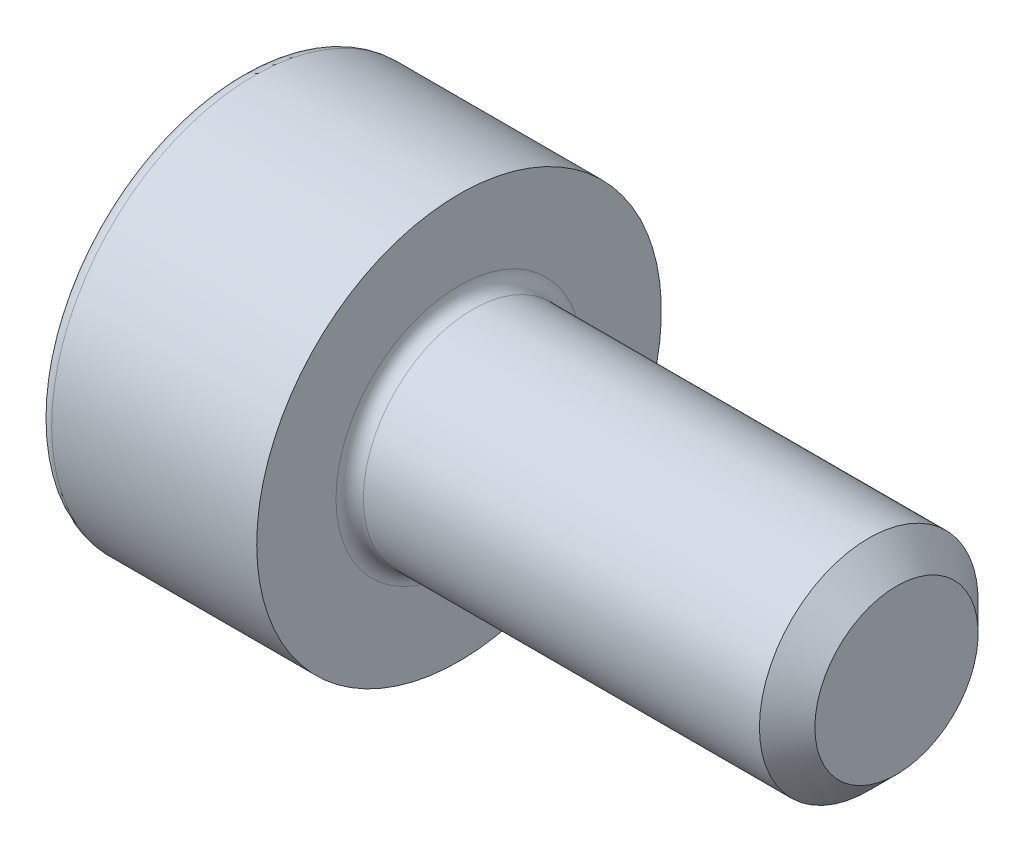
SolidWorks part; units mm, degrees
ref_plane "Front" through (0, 0, 0) normal (0, 0, 1) x (1, 0, 0)
ref_plane "Top" through (0, 0, 0) normal (0, 1, 0) x (1, 0, 0)
ref_plane "Right" through (0, 0, 0) normal (1, 0, 0) x (0, 0, -1)
sketch "Sketch1" plane through (0, 0, 0) normal (0, 0, 1) x (1, 0, 0)
  line L0 (3.7465, 1) -> (0.125, 1)
  line L1 (-2, 1.725) -> (-2, 0)
  line L2 (0, 1.85) -> (-1.875, 1.85)
  line L3 (0, 1.125) -> (0, 1.85)
  line L4 (4, 0.7465) -> (4, 0)
  line L5 (4, 0.7465) -> (3.7465, 1)
  line L6 (-2, 0) -> (0, 0) construction
  line L7 (-2, 0) -> (4, 0)
  arc A0 (-1.875, 1.85) -> (-2, 1.725) centre (-1.875, 1.725) ccw
  arc A1 (0, 1.125) -> (0.125, 1) centre (0.125, 1.125) ccw
  point P12 (0, 1.4875)
  dimension "D5" = 0.125
  dimension "D1" = 2
  dimension "D2" = 3.7
  dimension "D3" = 135
  dimension "D4" = 0.3585
  dimension "D6" = 4
  dimension "D7" = 2
revolve "Revolve1" add sketch "Sketch1" angle 360 about L7
sketch "Sketch2" plane through (-2, 0, 0) normal (-1, 0, 0) x (0, 0, 1)
  line L7 (0.75, 0.433) -> (0, 0.866)
  line L8 (0, 0.866) -> (-0.75, 0.433)
  line L9 (-0.75, 0.433) -> (-0.75, -0.433)
  line L10 (-0.75, -0.433) -> (0, -0.866)
  line L11 (0, -0.866) -> (0.75, -0.433)
  line L12 (0.75, -0.433) -> (0.75, 0.433)
  circle A0 centre (0, 0) radius 0.75 construction
  dimension "D1" = 1.5
extrude "Cut-Extrude1" cut sketch "Sketch2" against normal blind 1.1
